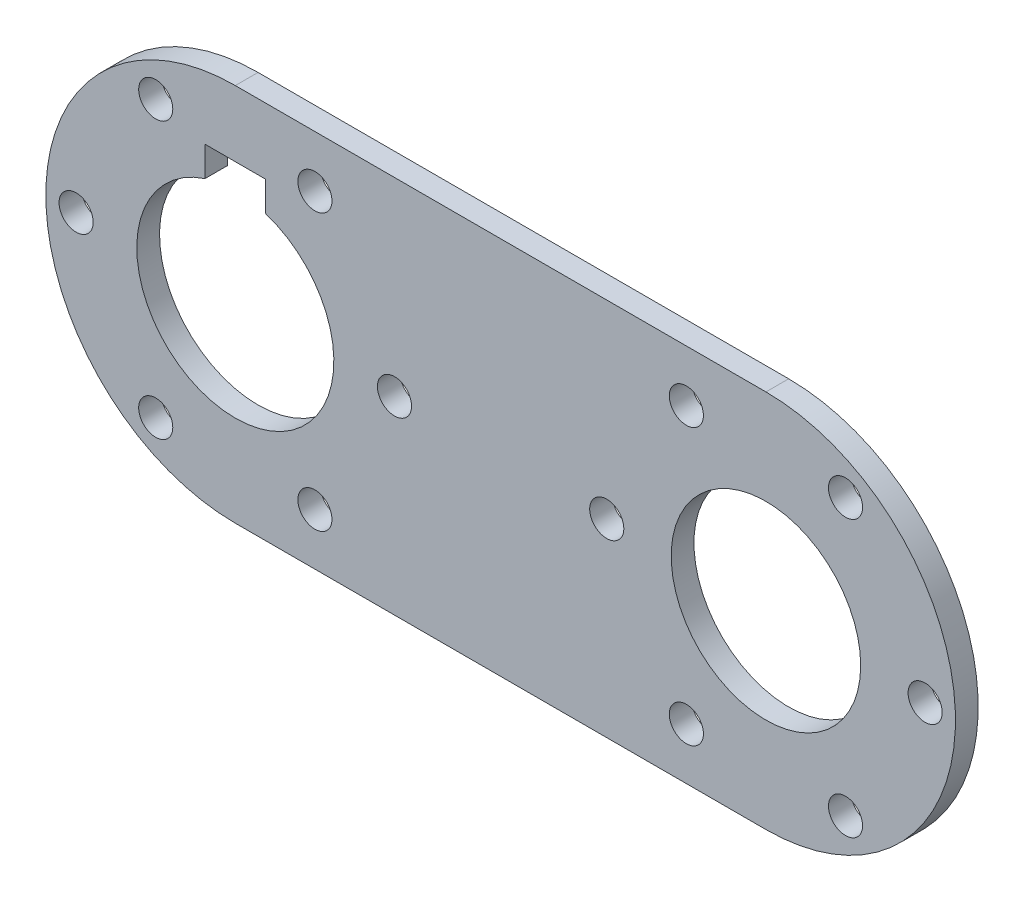
SolidWorks part; units mm, degrees
ref_plane "Alzado" through (0, 0, 0) normal (0, 0, 1) x (1, 0, 0)
ref_plane "Planta" through (0, 0, 0) normal (0, 1, 0) x (1, 0, 0)
ref_plane "Vista lateral" through (0, 0, 0) normal (1, 0, 0) x (0, 0, -1)
sketch "Croquis1" plane through (0, 0, 0) normal (0, 0, 1) x (1, 0, 0)
  line L0 (0, 0) -> (70, 0) construction
  line L1 (0, 25) -> (70, 25)
  line L2 (70, -25) -> (0, -25)
  circle A0 centre (0, 0) radius 25
  circle A1 centre (70, 0) radius 25
  circle A2 centre (70, 0) radius 12.5
  dimension "D1" = 50
  dimension "D2" = 50
  dimension "D4" = 25
  dimension "D3" = 70
extrude "Saliente-Extruir1" add sketch "Croquis1" along normal blind 3
hole_wizard "Taladro de margen para M42" positions "Croquis4" profile "Croquis5" hole size "M4" standard "ISO" end condition through all
sketch "Croquis4" plane through (0, 0, 3) normal (0, 0, 1) x (1, 0, 0)
  circle A0 centre (70, 0) radius 12.5 construction
  point P0 (-21, 0)
  point P2 (91, 0)
  point P14 (-10.5, 18.1865)
  point P15 (10.5, 18.1865)
  point P16 (21, 0)
  point P17 (10.5, -18.1865)
  point P18 (-10.5, -18.1865)
  point P26 (80.5, -18.1865)
  point P27 (59.5, -18.1865)
  point P28 (49, 0)
  point P29 (59.5, 18.1865)
  point P30 (80.5, 18.1865)
  dimension "D1" = 21
  dimension "D2" = 21
  dimension "D3" = 6
  dimension "D4" = 6
sketch "Croquis5" plane through (-21, 0, 3) normal (1, 0, 0) x (0, -1, 0)
  line L0 (0, 0) -> (0, 3)
  line L1 (0, 3) -> (2.25, 3)
  line L2 (2.25, 3) -> (2.25, 0)
  line L5 (2.25, 0) -> (0, 0)
  line L11 (0, -6.35) -> (0, 107.95) construction
  dimension "Diámetro de taladro hasta el siguiente" = 4.5
  dimension "Profundidad de taladro hasta el siguiente" = 3
sketch "KeySketch" plane through (0.8375, -0.4745, 3) normal (0, 0, 1) x (1, 0, 0)
  line L0 (-0.8375, -12.5255) -> (-0.8375, 16.7745) construction
  line L1 (-13.8375, 0.4745) -> (12.1625, 0.4745) construction
  line L2 (-4.8375, 12.8438) -> (-4.8375, 16.7745)
  line L4 (3.1625, 16.7745) -> (3.1625, 12.8438)
  line L5 (3.1625, 16.7745) -> (-4.8375, 16.7745)
  arc A0 (-4.8375, 12.8438) -> (3.1625, 12.8438) centre (-0.8375, 0.4745) ccw
  circle A1 centre (-0.8375, 0.4745) radius 25 construction
  point P10 (-0.8375, 16.7745)
  dimension "Diameter" = 26
  dimension "Width" = 8
  dimension "Depth" = 3.3
extrude "Keyway" cut sketch "KeySketch" against normal through all
other "bore with deep pattern keyway din 6886 p1<1>"
